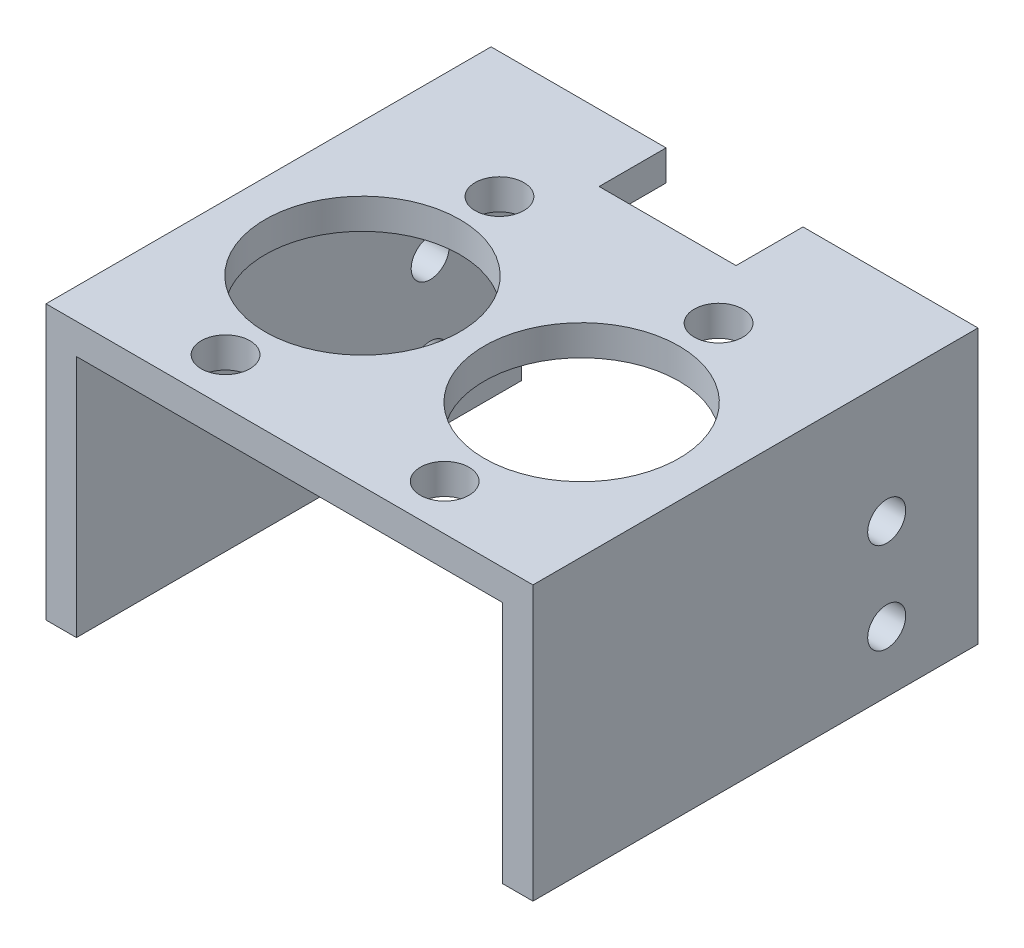
SolidWorks part; units mm, degrees
ref_plane "Front Plane" through (0, 0, 0) normal (0, 0, 1) x (1, 0, 0)
ref_plane "Top Plane" through (0, 0, 0) normal (0, 1, 0) x (1, 0, 0)
ref_plane "Right Plane" through (0, 0, 0) normal (1, 0, 0) x (0, 0, -1)
sketch "Sketch1" plane through (0, 0, 0) normal (0, 0, 1) x (1, 0, 0)
  line L1 (-112.6187, 0.1034) -> (-106.2687, 0.1034)
  line L2 (-112.6187, 0.1034) -> (-112.6187, 57.2534)
  line L3 (-112.6187, 57.2534) -> (-106.2687, 57.2534)
  line L4 (-106.2687, 0.1034) -> (-106.2687, 57.2534)
  line L5 (-106.2687, 57.2534) -> (-17.3687, 57.2534)
  line L6 (-106.2687, 57.2534) -> (-106.2687, 50.9034)
  line L7 (-106.2687, 50.9034) -> (-17.3687, 50.9034)
  line L8 (-17.3687, 57.2534) -> (-17.3687, 50.9034)
  line L9 (-17.3687, 57.2534) -> (-11.0187, 57.2534)
  line L10 (-17.3687, 57.2534) -> (-17.3687, 0.1034)
  line L11 (-17.3687, 0.1034) -> (-11.0187, 0.1034)
  line L12 (-11.0187, 57.2534) -> (-11.0187, 0.1034)
  dimension "D1" = 101.6
  dimension "D2" = 6.35
  dimension "D3" = 6.35
  dimension "D4" = 57.15
  dimension "D5" = 6.35
extrude "Boss-Extrude1" add sketch "Sketch1" along normal blind 92.8649 contours L1 L4 L3 L2 | L8 L5 L4 L7 | L12 L9 L8 L10 L11
sketch "Sketch2" plane through (0, 57.2534, 0) normal (0, 1, 0) x (1, 0, 0)
  line L0 (-61.8187, 0) -> (-61.8187, -92.8649) construction
  line L1 (-112.6187, 0) -> (-11.0187, 0) construction
  line L2 (-112.6187, -92.8649) -> (-11.0187, -92.8649) construction
  line L3 (-112.6187, -46.4325) -> (-61.8187, -46.4325) construction
  line L4 (-76.1062, 0) -> (-47.5312, 0)
  line L5 (-76.1062, -13.97) -> (-47.5312, -13.97)
  line L6 (-112.6187, -92.8649) -> (-112.6187, 0) construction
  line L7 (-61.8187, -46.4325) -> (-11.0187, -46.4325) construction
  line L8 (-11.0187, -92.8649) -> (-11.0187, 0) construction
  line L9 (-84.6787, -26.1899) -> (-84.6787, -83.3399) construction
  line L10 (-38.9587, -26.1899) -> (-38.9587, -83.3399) construction
  line L11 (-76.1062, -13.97) -> (-76.1062, 0)
  line L12 (-47.5312, -13.97) -> (-47.5312, 0)
  line L13 (-76.1062, -6.985) -> (-47.5312, -6.985) construction
  line L14 (-76.1062, 0) -> (-76.1062, -6.985) construction
  line L15 (-47.5312, 0) -> (-47.5312, -6.985) construction
  line L16 (-69.1212, -13.97) -> (-54.5162, -13.97)
  circle A0 centre (-38.9587, -54.7649) radius 20.32
  circle A1 centre (-84.6787, -54.7649) radius 20.32
  circle A2 centre (-84.6787, -26.1899) radius 5.08
  circle A3 centre (-84.6787, -83.3399) radius 5.08
  circle A4 centre (-38.9587, -26.1899) radius 5.08
  circle A5 centre (-38.9587, -83.3399) radius 5.08
  circle A6 centre (-84.6787, -26.1899) radius 9.525 construction
  circle A7 centre (-38.9587, -26.1899) radius 9.525 construction
  circle A8 centre (-84.6787, -83.3399) radius 9.525 construction
  circle A9 centre (-38.9587, -83.3399) radius 9.525 construction
  circle A10 centre (-69.1212, -6.985) radius 6.985 construction
  circle A11 centre (-54.5162, -6.985) radius 6.985 construction
  arc A12 (-69.1212, -13.97) -> (-76.1062, -6.985) centre (-69.1212, -6.985) cw construction
  arc A13 (-54.5162, -13.97) -> (-47.5312, -6.985) centre (-54.5162, -6.985) ccw construction
  line M6 (-11.0187, 0) -> (-112.6187, 0)
  dimension "D1" = 40.64
  dimension "D2" = 40.64
  dimension "D5" = 10.16
  dimension "D6" = 10.16
  dimension "D7" = 10.16
  dimension "D8" = 10.16
  dimension "D11" = 19.05
  dimension "D12" = 19.05
  dimension "D13" = 19.05
  dimension "D14" = 19.05
  dimension "D18" = 13.97
  dimension "D19" = 13.97
  dimension "D3" = 57.15
  dimension "D4" = 57.15
  dimension "D9" = 22.86
  dimension "D10" = 22.86
  dimension "D15" = 14.2875
  dimension "D16" = 14.2875
  dimension "D17" = 6.985
extrude "Master Cylinder Mount" cut sketch "Sketch2" against normal up to next contours L5 L12 L11 M6 | A4 | A2 | A3 | A5 | A0 | A1
sketch "Sketch3" plane through (-112.6187, 0, 0) normal (-1, 0, 0) x (0, 0, 1)
  line L0 (0, 57.2534) -> (19.05, 57.2534) construction
  line L1 (0, 0.1034) -> (0, 57.2534) construction
  line L2 (92.8649, 0.1034) -> (0, 0.1034) construction
  line L3 (19.05, 57.2534) -> (19.05, 0.1034) construction
  circle A0 centre (19.05, 12.8034) radius 3.9688
  circle A1 centre (19.05, 31.8534) radius 3.9688
  dimension "D3" = 7.9375
  dimension "D4" = 7.9375
  dimension "D1" = 57.15
  dimension "D2" = 19.05
  dimension "D5" = 12.7
  dimension "D6" = 25.4
extrude "Bracket Mount" cut sketch "Sketch3" against normal through all
